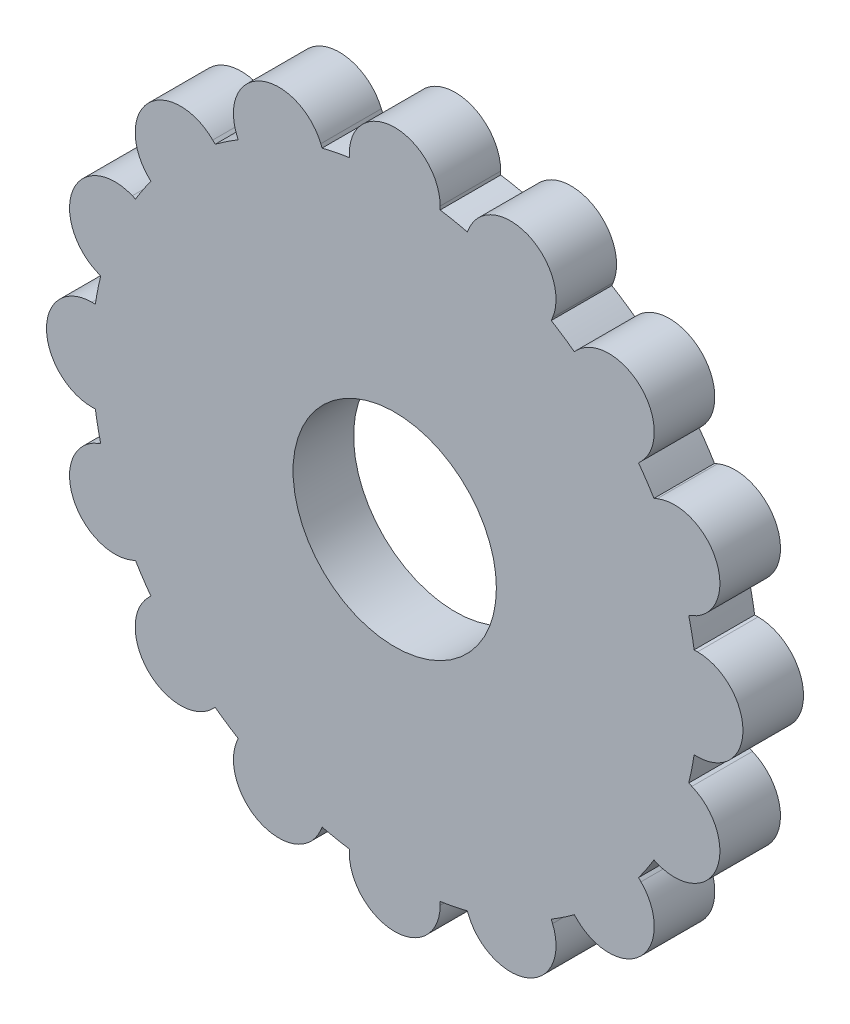
SolidWorks part; units mm, degrees
ref_plane "Front Plane" through (0, 0, 0) normal (0, 0, 1) x (1, 0, 0)
ref_plane "Top Plane" through (0, 0, 0) normal (0, 1, 0) x (1, 0, 0)
ref_plane "Right Plane" through (0, 0, 0) normal (1, 0, 0) x (0, 0, -1)
sketch "Sketch2" plane through (0, 0, 0) normal (0, 0, 1) x (1, 0, 0)
  line L0 (11.9886, 48.5415) -> (12.2051, 49.0641)
  line L1 (-7.5, 49.4343) -> (-7.5, 50)
  line L2 (7.5, 49.4343) -> (7.5, 50)
  line L3 (25.8468, 42.8012) -> (26.0633, 43.3239)
  line L4 (29.652, 40.2586) -> (30.052, 40.6586)
  line L5 (40.2586, 29.652) -> (40.6586, 30.052)
  line L6 (42.8012, 25.8468) -> (43.3239, 26.0633)
  line L7 (48.5415, 11.9886) -> (49.0641, 12.2051)
  line L8 (49.4343, 7.5) -> (50, 7.5)
  line L9 (49.4343, -7.5) -> (50, -7.5)
  line L10 (48.5415, -11.9886) -> (49.0641, -12.2051)
  line L11 (42.8012, -25.8468) -> (43.3239, -26.0633)
  line L12 (40.2586, -29.652) -> (40.6586, -30.052)
  line L13 (29.652, -40.2586) -> (30.052, -40.6586)
  line L14 (25.8468, -42.8012) -> (26.0633, -43.3239)
  line L15 (11.9886, -48.5415) -> (12.2051, -49.0641)
  line L16 (7.5, -49.4343) -> (7.5, -50)
  line L17 (-7.5, -49.4343) -> (-7.5, -50)
  line L18 (-11.9886, -48.5415) -> (-12.2051, -49.0641)
  line L19 (-25.8468, -42.8012) -> (-26.0633, -43.3239)
  line L20 (-29.652, -40.2586) -> (-30.052, -40.6586)
  line L21 (-40.2586, -29.652) -> (-40.6586, -30.052)
  line L22 (-42.8012, -25.8468) -> (-43.3239, -26.0633)
  line L23 (-48.5415, -11.9886) -> (-49.0641, -12.2051)
  line L24 (-49.4343, -7.5) -> (-50, -7.5)
  line L25 (-49.4343, 7.5) -> (-50, 7.5)
  line L26 (-48.5415, 11.9886) -> (-49.0641, 12.2051)
  line L27 (-42.8012, 25.8468) -> (-43.3239, 26.0633)
  line L28 (-40.2586, 29.652) -> (-40.6586, 30.052)
  line L29 (-29.652, 40.2586) -> (-30.052, 40.6586)
  line L30 (-25.8468, 42.8012) -> (-26.0633, 43.3239)
  line L31 (-11.9886, 48.5415) -> (-12.2051, 49.0641)
  arc A0 (-7.5, 49.4343) -> (7.5, 49.4343) centre (0, 0) ccw
  arc A2 (7.5, 50) -> (-7.5, 50) centre (0, 50) ccw
  arc A3 (26.0633, 43.3239) -> (12.2051, 49.0641) centre (19.1342, 46.194) ccw
  arc A4 (11.9886, 48.5415) -> (25.8468, 42.8012) centre (0, 0) ccw
  arc A5 (40.6586, 30.052) -> (30.052, 40.6586) centre (35.3553, 35.3553) ccw
  arc A6 (29.652, 40.2586) -> (40.2586, 29.652) centre (0, 0) ccw
  arc A7 (49.0641, 12.2051) -> (43.3239, 26.0633) centre (46.194, 19.1342) ccw
  arc A8 (42.8012, 25.8468) -> (48.5415, 11.9886) centre (0, 0) ccw
  arc A9 (50, -7.5) -> (50, 7.5) centre (50, 0) ccw
  arc A10 (49.4343, 7.5) -> (49.4343, -7.5) centre (0, 0) ccw
  arc A11 (43.3239, -26.0633) -> (49.0641, -12.2051) centre (46.194, -19.1342) ccw
  arc A12 (48.5415, -11.9886) -> (42.8012, -25.8468) centre (0, 0) ccw
  arc A13 (30.052, -40.6586) -> (40.6586, -30.052) centre (35.3553, -35.3553) ccw
  arc A14 (40.2586, -29.652) -> (29.652, -40.2586) centre (0, 0) ccw
  arc A15 (12.2051, -49.0641) -> (26.0633, -43.3239) centre (19.1342, -46.194) ccw
  arc A16 (25.8468, -42.8012) -> (11.9886, -48.5415) centre (0, 0) ccw
  arc A17 (-7.5, -50) -> (7.5, -50) centre (0, -50) ccw
  arc A18 (7.5, -49.4343) -> (-7.5, -49.4343) centre (0, 0) ccw
  arc A19 (-26.0633, -43.3239) -> (-12.2051, -49.0641) centre (-19.1342, -46.194) ccw
  arc A20 (-11.9886, -48.5415) -> (-25.8468, -42.8012) centre (0, 0) ccw
  arc A21 (-40.6586, -30.052) -> (-30.052, -40.6586) centre (-35.3553, -35.3553) ccw
  arc A22 (-29.652, -40.2586) -> (-40.2586, -29.652) centre (0, 0) ccw
  arc A23 (-49.0641, -12.2051) -> (-43.3239, -26.0633) centre (-46.194, -19.1342) ccw
  arc A24 (-42.8012, -25.8468) -> (-48.5415, -11.9886) centre (0, 0) ccw
  arc A25 (-50, 7.5) -> (-50, -7.5) centre (-50, 0) ccw
  arc A26 (-49.4343, -7.5) -> (-49.4343, 7.5) centre (0, 0) ccw
  arc A27 (-43.3239, 26.0633) -> (-49.0641, 12.2051) centre (-46.194, 19.1342) ccw
  arc A28 (-48.5415, 11.9886) -> (-42.8012, 25.8468) centre (0, 0) ccw
  arc A29 (-30.052, 40.6586) -> (-40.6586, 30.052) centre (-35.3553, 35.3553) ccw
  arc A30 (-40.2586, 29.652) -> (-29.652, 40.2586) centre (0, 0) ccw
  arc A31 (-12.2051, 49.0641) -> (-26.0633, 43.3239) centre (-19.1342, 46.194) ccw
  arc A32 (-25.8468, 42.8012) -> (-11.9886, 48.5415) centre (0, 0) ccw
  point P84 (0, 0)
extrude "Boss-Extrude1" add sketch "Sketch2" along normal blind 10 contours L31 A31 L30 A0 | A4 L2 A2 L1 | L3 A3 L0 A0 | L5 A5 L4 A0 | L7 A7 L6 A0 | L9 A9 L8 A0 | L11 A11 L10 A0 | L13 A13 L12 A0 | L15 A15 L14 A0 | L17 A17 L16 A0 | L19 A19 L18 A0 | L21 A21 L20 A0 | L23 A23 L22 A0 | L25 A25 L24 A0 | L27 A27 L26 A0 | L28 A29 L29 A30
sketch "Sketch3" plane through (0, 0, 0) normal (0, 0, 1) x (1, 0, 0)
  circle A0 centre (0, 0) radius 16.787
extrude "Cut-Extrude6" cut sketch "Sketch3" against normal blind 35 and the other way through all contours A0
